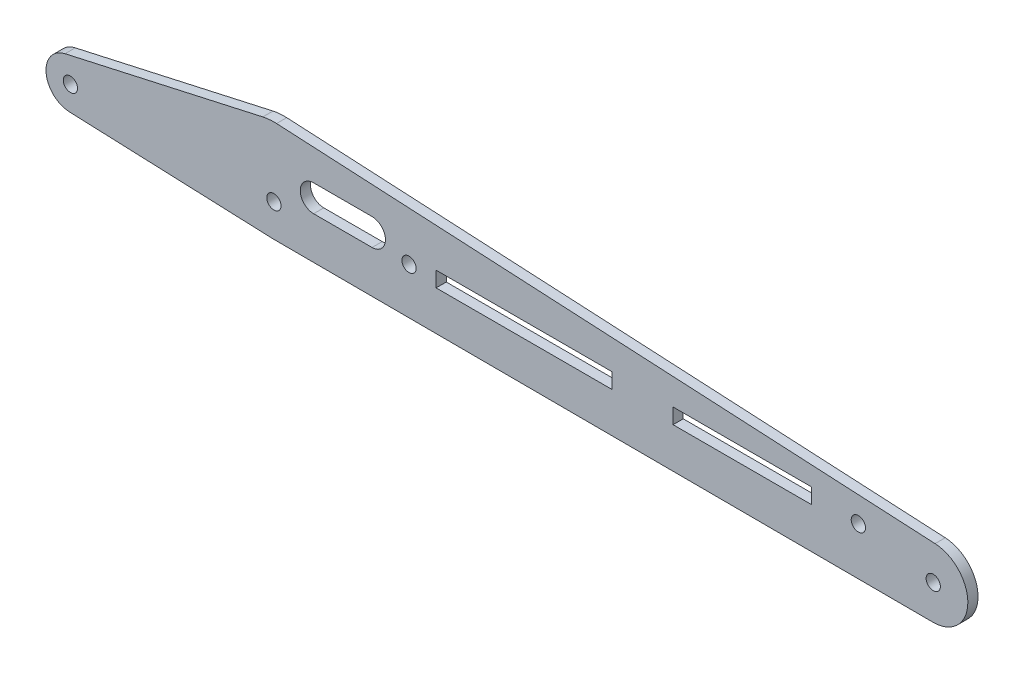
SolidWorks part; units mm, degrees
ref_plane "前视基准面" through (0, 0, 0) normal (0, 0, 1) x (1, 0, 0)
ref_plane "上视基准面" through (0, 0, 0) normal (0, 1, 0) x (1, 0, 0)
ref_plane "右视基准面" through (0, 0, 0) normal (1, 0, 0) x (0, 0, -1)
sketch "草图1" plane through (0, 0, 0) normal (0, 0, 1) x (1, 0, 0)
  line L0 (0, 0) -> (50, 0) construction
  line L1 (212, 0) -> (50, 0) construction
  line L2 (0, -6) -> (50, -6) construction
  line L3 (50, 17) -> (50, -8) construction
  line L4 (50, -6) -> (50, 0) construction
  line L5 (-0.2404, -5.9952) -> (49.4991, -7.99)
  line L6 (47.277, 16.6998) -> (-1.307, 5.8559)
  line L7 (211.9738, -8.5) -> (49.9614, -7.9999)
  line L8 (50.3279, 17) -> (212.4457, 8.4883)
  line L9 (50.3279, 17) -> (50, 17)
  circle A0 centre (0, 0) radius 1.75
  circle A1 centre (50, 0) radius 1.75
  circle A2 centre (212, 0) radius 1.75
  arc A3 (-1.307, 5.8559) -> (0, -6) centre (0, 0) ccw
  arc A5 (211.9738, -8.5) -> (212.4457, 8.4883) centre (212, 0) ccw
  arc A6 (49.4991, -7.99) -> (50, -8) centre (50, 4.5) ccw
  arc A7 (50.6554, 16.9828) -> (47.277, 16.6998) centre (50, 4.5) ccw
  dimension "D1" = 3.5
  dimension "D2" = 3.5
  dimension "D4" = 3.5
  dimension "D6" = 12
  dimension "D7" = 25
  dimension "D8" = 17
  dimension "D3" = 50
  dimension "D5" = 212
  dimension "D9" = 2
extrude "凸台-拉伸2" add sketch "草图1" along normal blind 2.5
sketch "草图2" plane through (0, 0, 2.5) normal (0, 0, 1) x (1, 0, 0)
  line L0 (59.7582, 5.6266) -> (74.1156, 5.6266) construction
  line L3 (59.7582, 8.9145) -> (74.1156, 8.9145)
  line L4 (59.7582, 2.3386) -> (74.1156, 2.3386)
  line L5 (111.4403, 3.4902) -> (165.0792, 3.4902) construction
  line L11 (89.8528, 1.6049) -> (133.0278, 1.6049)
  line L16 (89.8528, 1.6049) -> (89.8528, 5.3755)
  line L17 (89.8528, 5.3755) -> (133.0278, 5.3755)
  line L18 (133.0278, 1.6049) -> (133.0278, 5.3755)
  line L19 (89.8528, 1.6049) -> (133.0278, 5.3755) construction
  line L20 (89.8528, 5.3755) -> (133.0278, 1.6049) construction
  line L21 (148.0719, 1.6049) -> (182.0865, 1.6049)
  line L22 (148.0719, 1.6049) -> (148.0719, 5.3755)
  line L23 (148.0719, 5.3755) -> (182.0865, 5.3755)
  line L24 (182.0865, 1.6049) -> (182.0865, 5.3755)
  line L25 (148.0719, 1.6049) -> (182.0865, 5.3755) construction
  line L26 (148.0719, 5.3755) -> (182.0865, 1.6049) construction
  arc A2 (59.7582, 8.9145) -> (59.7582, 2.3386) centre (59.7582, 5.6266) ccw
  arc A3 (74.1156, 2.3386) -> (74.1156, 8.9145) centre (74.1156, 5.6266) ccw
  point P2 (66.9369, 5.6266)
  point P7 (111.4403, 3.4902)
extrude "切除-拉伸1" cut sketch "草图2" against normal through all
sketch "草图3" plane through (0, 0, 2.5) normal (0, 0, 1) x (1, 0, 0)
  line L0 (-27.2192, 3.287) -> (193.5958, 3.287)
  circle A0 centre (83.1883, 3.287) radius 1.75
  circle A1 centre (193.5958, 3.287) radius 1.75
  point P4 (83.1883, 3.287)
  dimension "D1" = 3.5
  dimension "D2" = 3.5
extrude "切除-拉伸2" cut sketch "草图3" against normal through all contours L0 A0 | A1
